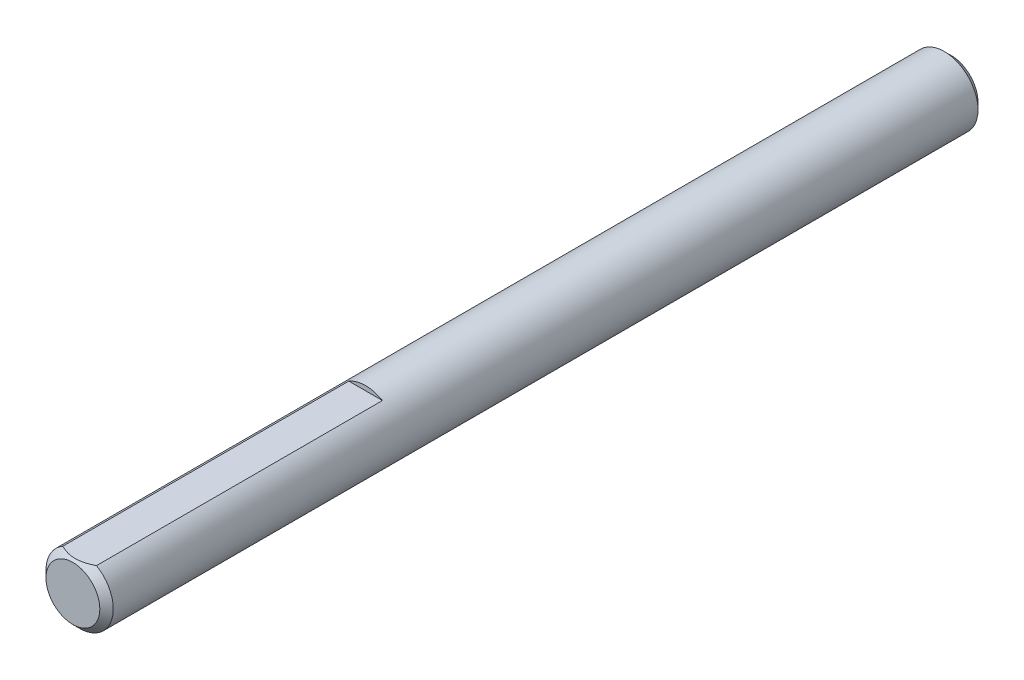
SolidWorks part; units mm, degrees
ref_plane "Front" through (0, 0, 0) normal (0, 0, 1) x (1, 0, 0)
ref_plane "Top" through (0, 0, 0) normal (0, 1, 0) x (1, 0, 0)
ref_plane "Right" through (0, 0, 0) normal (1, 0, 0) x (0, 0, -1)
sketch "Sketch1" plane through (0, 0, 0) normal (0, 0, 1) x (1, 0, 0)
  circle A0 centre (0, 0) radius 2.921
  dimension "D1" = 5.842
extrude "Extrude1" add sketch "Sketch1" along normal mid plane 76.2
chamfer "Chamfer1" distance 0.5842 angle 45 2 edges at (2.921, 0, -38.1) (2.921, 0, 38.1)
ref_plane "Plane1" through (0, 0, 12.7) normal (0, 0, 1) x (1, 0, 0)
sketch "Sketch13" plane through (0, 0, 12.7) normal (0, 0, 1) x (1, 0, 0)
  line L3 (-1.4605, 2.5297) -> (1.4605, 2.5297)
  circle A0 centre (0, 0) radius 2.921 construction
  arc A1 (1.4605, 2.5297) -> (-1.4605, 2.5297) centre (0, 0) ccw
  dimension "D1" = 2.921
extrude "Extrude7" cut sketch "Sketch13" along normal through all
equation "\"D1@Chamfer1\" = \"D1@Sketch1\" * .1"
equation "\"D1@Sketch13\" = \"D1@Sketch1\" * .5"
